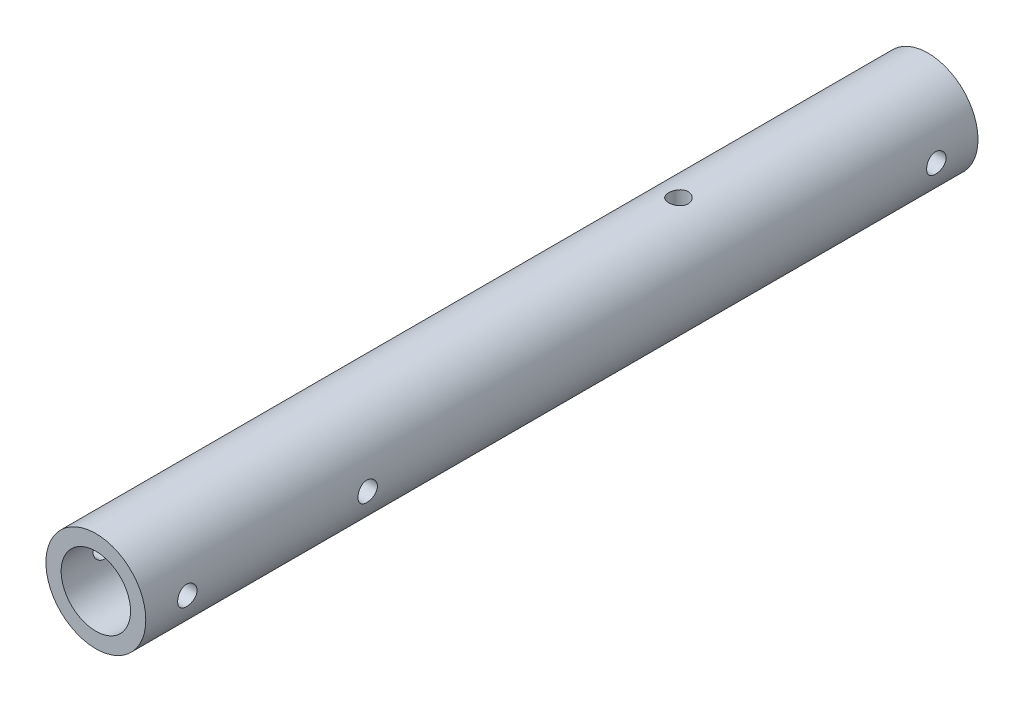
SolidWorks part; units mm, degrees
material "ﾎﾟﾘ塩化ﾋﾞﾆﾙ(PVC)硬質"
ref_plane "正面(Front)" through (0, 0, 0) normal (0, 0, 1) x (1, 0, 0)
ref_plane "平面(Top)" through (0, 0, 0) normal (0, 1, 0) x (1, 0, 0)
ref_plane "右側面(Right)" through (0, 0, 0) normal (1, 0, 0) x (0, 0, -1)
sketch "ｽｹｯﾁ1" plane through (0, 0, 0) normal (0, 0, 1) x (1, 0, 0)
  circle A0 centre (0, 0) radius 9
  circle A1 centre (0, 0) radius 6.25
  dimension "D1" = 18
  dimension "D2" = 12.5
extrude "ﾎﾞｽ - 押し出し1" add sketch "ｽｹｯﾁ1" along normal blind 150
sketch "ｽｹｯﾁ2" plane through (0, 0, 0) normal (1, 0, 0) x (0, 0, -1)
  line L0 (0, 0) -> (-231.2557, 0) construction
  line L1 (0, -9) -> (0, 9) construction
  line L2 (-150, 9) -> (-150, -9) construction
  circle A0 centre (-7.5, 0) radius 1.75
  circle A1 centre (-142.5, 0) radius 1.75
  circle A2 centre (-110, 0) radius 1.75
  dimension "D2" = 7.5
  dimension "D3" = 3.5
  dimension "D1" = 7.5
  dimension "D4" = 40
extrude "ｶｯﾄ - 押し出し1" cut sketch "ｽｹｯﾁ2" against normal through all both and the other way through all
sketch "ｽｹｯﾁ3" plane through (0, 0, 0) normal (0, 1, 0) x (1, 0, 0)
  line L0 (0, 0) -> (0, -220.1944) construction
  line L1 (9, 0) -> (-9, 0) construction
  circle A0 centre (0, -45) radius 1.75
  dimension "D1" = 3.5
  dimension "D2" = 45
extrude "ｶｯﾄ - 押し出し2" cut sketch "ｽｹｯﾁ3" against normal through all both and the other way through all
